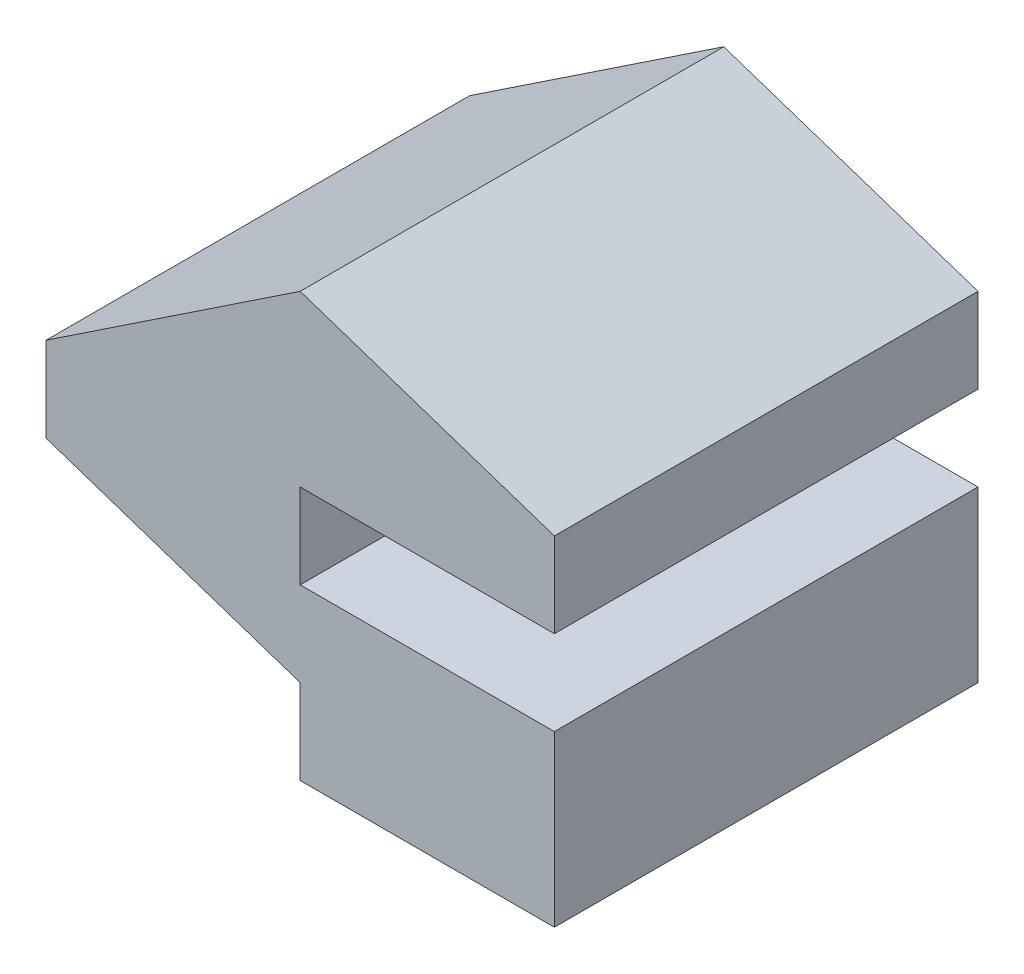
SolidWorks part; units mm, degrees
ref_plane "Front Plane" through (0, 0, 0) normal (0, 0, 1) x (1, 0, 0)
ref_plane "Top Plane" through (0, 0, 0) normal (0, 1, 0) x (1, 0, 0)
ref_plane "Right Plane" through (0, 0, 0) normal (1, 0, 0) x (0, 0, -1)
sketch "Sketch26" plane through (0, 0, 0) normal (0, 0, 1) x (1, 0, 0)
  line L0 (0, 0) -> (0, 1)
  line L1 (0, 1) -> (-3, 2)
  line L2 (-3, 2) -> (-3, 3)
  line L3 (-3, 3) -> (0, 5)
  line L4 (0, 5) -> (3, 4)
  line L5 (3, 4) -> (3, 3)
  line L6 (3, 3) -> (0, 3)
  line L7 (0, 3) -> (0, 2)
  line L8 (0, 2) -> (3, 2)
  line L9 (3, 2) -> (3, 0)
  line L10 (3, 0) -> (0, 0)
  dimension "D1" = 1
  dimension "D2" = 1
  dimension "D3" = 1
  dimension "D4" = 2
  dimension "D5" = 1
  dimension "D6" = 2
  dimension "D7" = 3
  dimension "D8" = 3
  dimension "D9" = 3
extrude "Boss-Extrude16" add sketch "Sketch26" along normal blind 5
